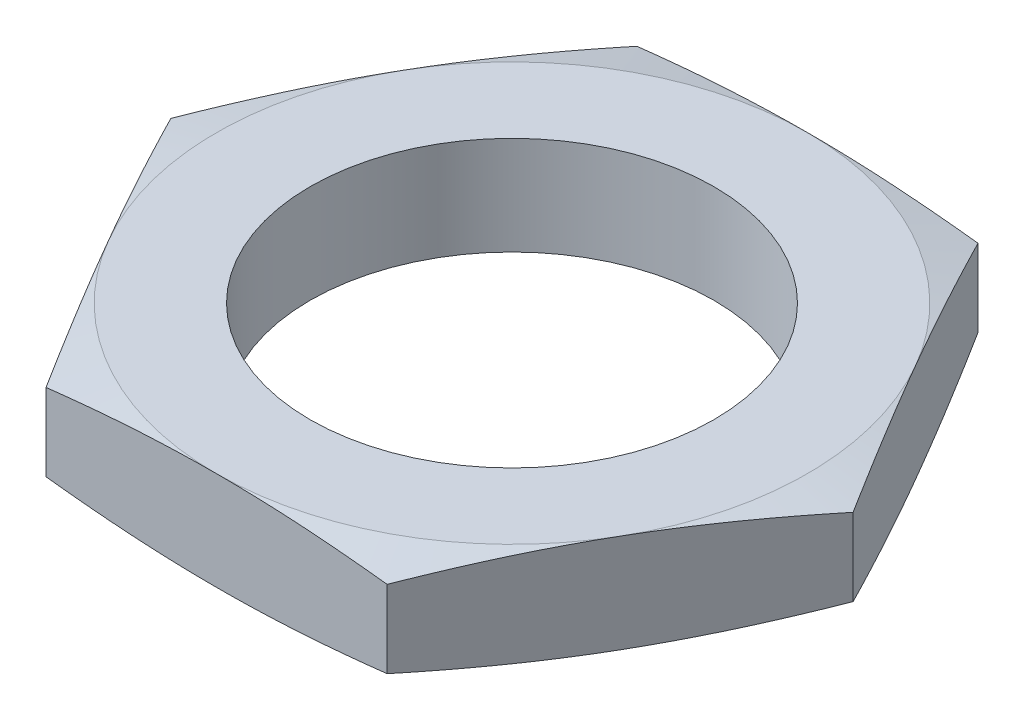
SolidWorks part; units mm, degrees
material "1060 Сплав"
ref_plane "Спереди" through (0, 0, 0) normal (0, 0, 1) x (1, 0, 0)
ref_plane "Сверху" through (0, 0, 0) normal (0, 1, 0) x (1, 0, 0)
ref_plane "Справа" through (0, 0, 0) normal (1, 0, 0) x (0, 0, -1)
sketch "Эскиз1" plane through (0, 0, 0) normal (0, 1, 0) x (1, 0, 0)
  line L1 (17.3205, 0) -> (8.6603, 15)
  line L2 (8.6603, 15) -> (-8.6603, 15)
  line L3 (-8.6603, 15) -> (-17.3205, 0)
  line L4 (-17.3205, 0) -> (-8.6603, -15)
  line L5 (-8.6603, -15) -> (8.6603, -15)
  line L6 (8.6603, -15) -> (17.3205, 0)
  circle A0 centre (0, 0) radius 15 construction
  circle A1 centre (0, 0) radius 10.25
  dimension "D1" = 30
  dimension "D2" = 20.5
extrude "Бобышка-Вытянуть1" add sketch "Эскиз1" along normal blind 5
cosmetic thread "Условное изображение резьбы1" parameters "D2"=22
sketch "Эскиз2" plane through (0, 5, 0) normal (0, 1, 0) x (1, 0, 0)
  line L0 (17.3205, 0) -> (8.6603, 15) construction
  circle A0 centre (0, 0) radius 15
extrude "Вырез-Вытянуть1" cut sketch "Эскиз2" against normal through all draft 77 flip side to cut
sketch "Эскиз3" plane through (0, 0, 0) normal (0, -1, 0) x (1, 0, 0)
  line L0 (-17.3205, 0) -> (-8.6603, 15) construction
  circle A0 centre (0, 0) radius 15
extrude "Вырез-Вытянуть2" cut sketch "Эскиз3" against normal through all draft 77 flip side to cut
